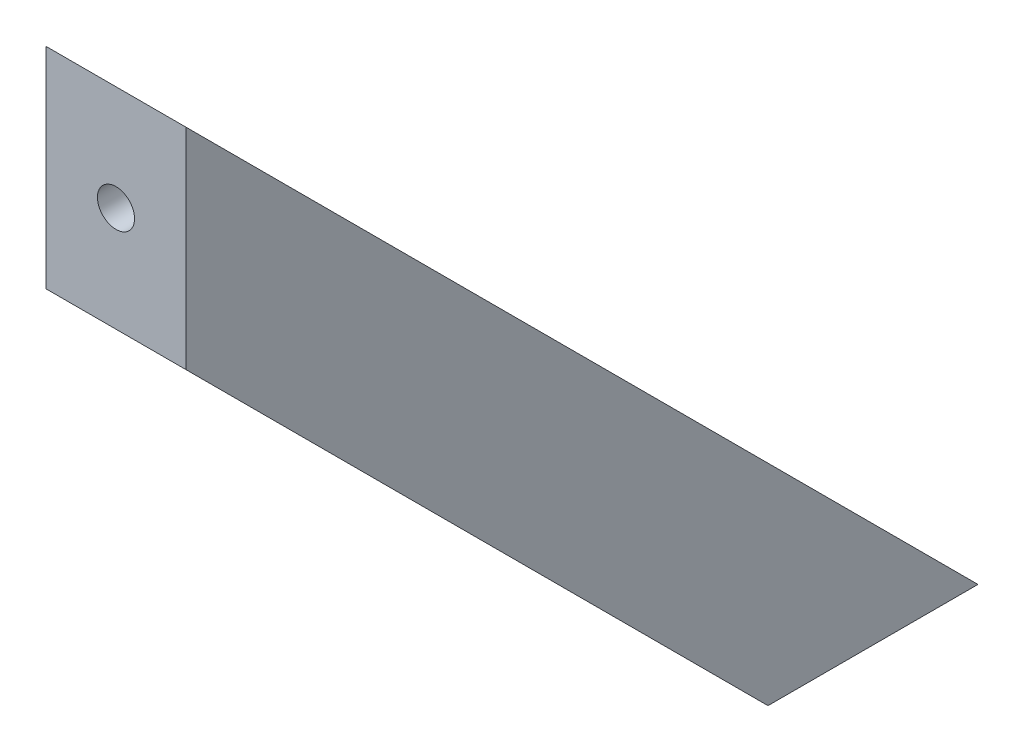
SolidWorks part; units mm, degrees
ref_plane "Front Plane" through (0, 0, 0) normal (0, 0, 1) x (1, 0, 0)
ref_plane "Top Plane" through (0, 0, 0) normal (0, 1, 0) x (1, 0, 0)
ref_plane "Right Plane" through (0, 0, 0) normal (1, 0, 0) x (0, 0, -1)
sketch "Sketch2" plane through (0, 0, 0) normal (1, 0, 0) x (0, 0, -1)
  line L6 (0, 0) -> (-83.1371, 83.1371)
  line L7 (-83.1371, 83.1371) -> (-83.1371, 113.1371)
  line L8 (-83.1371, 113.1371) -> (30, 0)
  line L9 (30, 0) -> (0, 0)
  dimension "D1" = 30
  dimension "D2" = 45
  dimension "D3" = 30
  dimension "D4" = 160
extrude "Boss-Extrude1" add sketch "Sketch2" along normal blind 20
sketch "Sketch3" plane through (0, 0, 0) normal (0, -1, 0) x (1, 0, 0)
  line L0 (10, 0) -> (10, -30) construction
  line L1 (20, 0) -> (0, 0) construction
  line L2 (20, -30) -> (0, -30) construction
  line L3 (0, -15) -> (20, -15) construction
  line L4 (0, 0) -> (0, -30) construction
  line L5 (20, 0) -> (20, -30) construction
  circle A0 centre (10, -15) radius 2.65
  dimension "D1" = 5.3
extrude "Cut-Extrude1" cut sketch "Sketch3" against normal through all
sketch "Sketch4" plane through (0, 0, 83.1371) normal (0, 0, 1) x (1, 0, 0)
  line L0 (10, 113.1371) -> (10, 83.1371) construction
  line L1 (20, 113.1371) -> (0, 113.1371) construction
  line L2 (20, 83.1371) -> (0, 83.1371) construction
  line L3 (0, 98.1371) -> (20, 98.1371) construction
  line L4 (0, 113.1371) -> (0, 83.1371) construction
  line L5 (20, 113.1371) -> (20, 83.1371) construction
  circle A0 centre (10, 98.1371) radius 2.65
  dimension "D1" = 5.3
extrude "Cut-Extrude2" cut sketch "Sketch4" against normal through all
ref_plane "Plane1" through (0, 0, 78.1371) normal (0, 0, 1) x (1, 0, 0)
sketch "Sketch5" plane through (0, 0, 78.1371) normal (0, 0, 1) x (1, 0, 0)
  circle A0 centre (10, 98.1371) radius 5.5
  dimension "D1" = 11
extrude "Cut-Extrude3" cut sketch "Sketch5" against normal through all
ref_plane "Plane2" through (0, 5, 0) normal (0, -1, 0) x (-1, 0, 0)
sketch "Sketch6" plane through (0, 5, 0) normal (0, -1, 0) x (-1, 0, 0)
  circle A0 centre (-10, 15) radius 5.5
  dimension "D1" = 11
extrude "Cut-Extrude4" cut sketch "Sketch6" against normal through all
